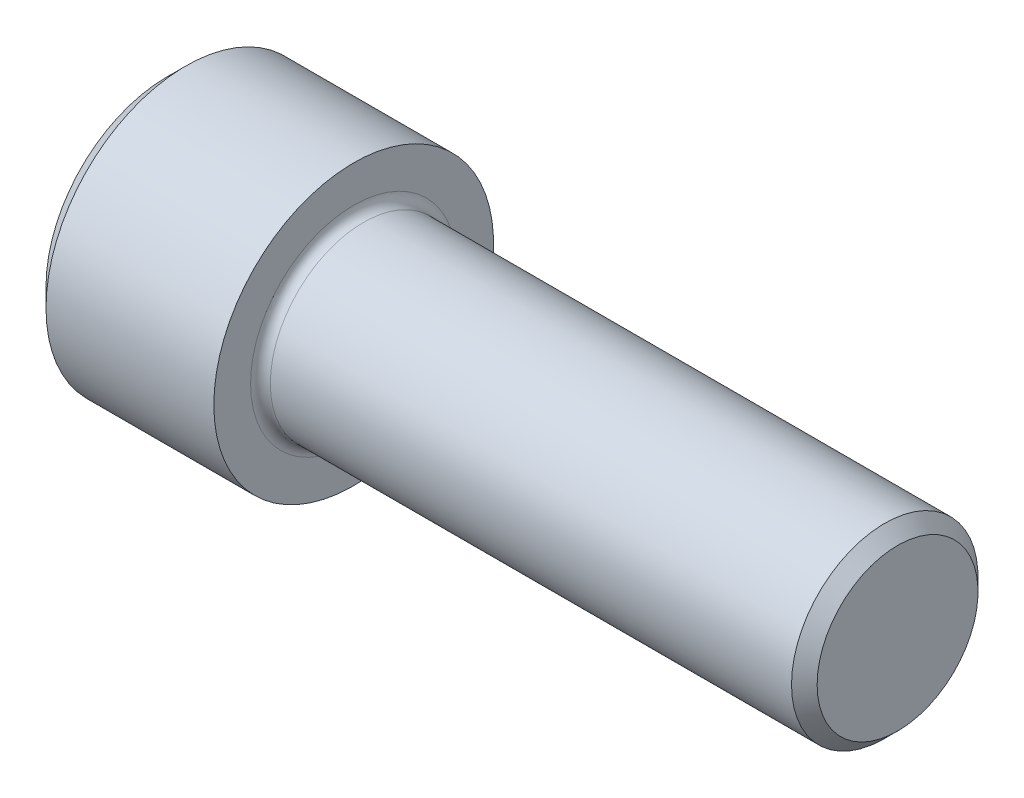
SolidWorks part; units mm, degrees
ref_plane "Plane1" through (0, 0, 0) normal (0, 0, 1) x (1, 0, 0)
ref_plane "Plane2" through (0, 0, 0) normal (0, 1, 0) x (1, 0, 0)
ref_plane "Plane3" through (0, 0, 0) normal (1, 0, 0) x (0, 0, -1)
sketch "BodySke" plane through (0, 0, 0) normal (0, 0, 1) x (1, 0, 0)
  line L0 (0, 0) -> (0, 15.6)
  line L1 (2.4, 18) -> (24, 18)
  line L2 (24, 18) -> (24, 12)
  line L3 (24, 12) -> (92.352, 12)
  line L4 (94, 10.352) -> (94, 0)
  line L5 (94, 0) -> (0, 0)
  line L6 (-31.75, 0) -> (127, 0) construction
  line L7 (0, 15.6) -> (2.4, 18)
  line L8 (94, 10.352) -> (92.352, 12)
  line L9 (0, -15.6) -> (2.4, -18) construction
  line L10 (94, -10.352) -> (92.352, -12) construction
  line L11 (27, 9.525) -> (27, 3.175) construction
  line L12 (44, 9.525) -> (44, 3.175) construction
  line L13 (44, 9.525) -> (44, 3.175) construction
  dimension "Diameter" = 24
  dimension "Head_ht" = 24
  dimension "Length" = 70
  dimension "Body_ch_ang" = 45
  dimension "Head_dia" = 36
  dimension "Head_ch_ang" = 45
  dimension "Minor_dia" = 20.704
  dimension "Advance" = 3
  dimension "Thread_nom" = 50
  dimension "Thread_length" = 50
  dimension "Head_ch_ht" = 2.4
revolve "Base-Revolve" add sketch "BodySke"
cosmetic thread "ThreadCosmetic"
fillet "Fillet1" radius 1.27 1 edges at (24, 0, 12)
sketch "Sketch2" plane through (0, 0, 0) normal (0, 0, 1) x (1, 0, 0)
  line L0 (0, 9.5) -> (12, 9.5)
  line L1 (12, 9.5) -> (17.4848, 0)
  line L2 (-31.75, 0) -> (127, 0) construction
  line L3 (17.4848, 0) -> (0, 0)
  line L4 (0, 0) -> (0, 9.5)
  line L5 (0, 15.6) -> (0, -15.6) construction
  line L6 (0, 0) -> (47.625, 0) construction
  line L7 (24, -18) -> (24, 18) construction
  dimension "D1" = 9.5
  dimension "D2" = 60
  dimension "Wall_thickness" = 12
revolve "Hex-PreBroach" cut sketch "Sketch2" angle 360 about L6
sketch "Sketch3" plane through (0, 0, 0) normal (-1, 0, 0) x (0, 0.5, 0.866)
  line L0 (5.4848, 9.5) -> (-5.4848, 9.5)
  line L1 (-5.4848, 9.5) -> (-10.9697, 0)
  line L2 (5.4848, 9.5) -> (10.9697, 0)
  line L3 (5.4848, -9.5) -> (10.9697, 0)
  line L4 (5.4848, -9.5) -> (-5.4848, -9.5)
  line L5 (-5.4848, -9.5) -> (-10.9697, 0)
  dimension "D1" = 9.5
  dimension "D2" = 9.5
  dimension "Hex_size" = 19
extrude "Hex" cut sketch "Sketch3" against normal blind 12
sketch "Sketch4" plane through (0, 0, 0) normal (-1, 0, 0) x (0, 0, 1)
  line L0 (0, 0) -> (10.1727, 0)
  line L1 (0, 0) -> (6.1484, 3.5498) construction
  line L2 (0, 0) -> (5.0863, 8.8098)
  line L3 (8.4417, 2.1022) -> (9.7612, 2.864)
  line L4 (6.0414, 6.2596) -> (7.3609, 7.0215)
  arc A0 (8.4417, 2.1022) -> (6.0414, 6.2596) centre (0, 0) ccw
  arc A1 (10.1727, 0) -> (9.7612, 2.864) centre (0, 0) ccw
  arc A2 (5.0863, 8.8098) -> (7.3609, 7.0215) centre (0, 0) cw
  dimension "D1" = 30
  dimension "Spline_n_dim" = 17.399
  dimension "Spline_m_dim" = 20.3454
  dimension "D2" = 60
  dimension "D3" = 2.4003
  dimension "Spline_p_dim" = 4.8006
extrude "Spline" [suppressed] cut sketch "Sketch4" against normal blind 12.573
pattern_circular "CirPattern1" [suppressed] count 6 every 60
sketch "Sketch5" plane through (0, 0, 0) normal (0, 0, 1) x (1, 0, 0)
  line L0 (-31.75, 0) -> (127, 0) construction
  line L2 (0, 15.6) -> (0, -15.6) construction
  circle A0 centre (7.3, 0) radius 1.075
  dimension "Drilled_hole_dia" = 2.15
  dimension "Drilled_hole_loc" = 7.3
extrude "Hole" [suppressed] cut sketch "Sketch5" against normal through all and the other way through all
pattern_circular "Drilled-4" [suppressed] count 2 every 60
pattern_circular "Drilled-6" [suppressed] count 3 every 60
sketch "ThdSchSke" plane through (0, 0, 0) normal (0, 0, 1) x (1, 0, 0)
  line L0 (44, -10.352) -> (42.8461, -12)
  line L1 (44, -10.352) -> (45.1539, -12)
  line L2 (45.1539, -12) -> (45.1539, -15)
  line L3 (-3.175, 0) -> (5.1513, 0) construction
  line L5 (45.1539, -15) -> (42.8461, -15)
  line L6 (42.8461, -15) -> (42.8461, -12)
  line L7 (0, 15.6) -> (0, -15.6) construction
  dimension "Thread_minor" = 20.704
  dimension "Diameter" = 24
  dimension "Start" = 44
  dimension "SideAngle" = 55
  dimension "VeeAngle" = 70
  dimension "Overcut" = 30
revolve "ThreadSchematic" [suppressed] cut sketch "ThdSchSke" angle 360 about L3
pattern_linear "ThdSchPat" [suppressed]
equation "\"D2@Sketch3\" = \"Hex_size@Sketch3\" / 2"
equation "\"D1@Sketch3\" = \"Hex_size@Sketch3\" / 2"
equation "\"D1@Sketch2\" = \"Hex_size@Sketch3\" / 2"
equation "\"D3@Sketch4\" = \"Spline_p_dim@Sketch4\" / 2"
equation "\"Thread_minor@ThreadCosmetic\"  =  \"Minor_dia@BodySke\""
equation "\"D2@CirPattern1\" = 360 / \"Num_teeth@CirPattern1\""
equation "\"Wall_thickness@Sketch2\" = \"Head_ht@BodySke\" - \"Key_eng@Hex\""
equation "\"Thread_length@ThreadCosmetic\" = ((sgn( (\"Length@BodySke\" - \"Advance@BodySke\" ) - \"Thread_nom@BodySke\" )-1)*( (\"Length@BodySke\" - \"Advance@BodySke\" ) - \"Thread_nom@BodySke\" ))/-2+ \"Thread_nom@BodySke\""
equation "\"Thread_minor@ThdSchSke\" = \"Minor_dia@BodySke\""
equation "\"Diameter@ThdSchSke\" = \"Diameter@BodySke\""
equation "\"Overcut@ThdSchSke\" = \"Diameter@BodySke\" * 1.25"
equation "\"Start@ThdSchSke\" = \"Head_ht@BodySke\" + \"Length@BodySke\" - \"Thread_length@ThreadCosmetic\"  '---Non-countersunk---"
equation "\"Num_threads@ThdSchPat\" = int( \"Thread_length@ThreadCosmetic\" / \"Advance@BodySke\" + 0.999 )  + 1"
equation "\"Advance@ThdSchPat\" = \"Thread_length@ThreadCosmetic\" /  (\"Num_threads@ThdSchPat\" - 1) 'relax it"
equation "\"Num_threads@ThdSchPat\" = \"Num_threads@ThdSchPat\" - sgn( \"Num_threads@ThdSchPat\" - 1) '---chamfered tips only---"
